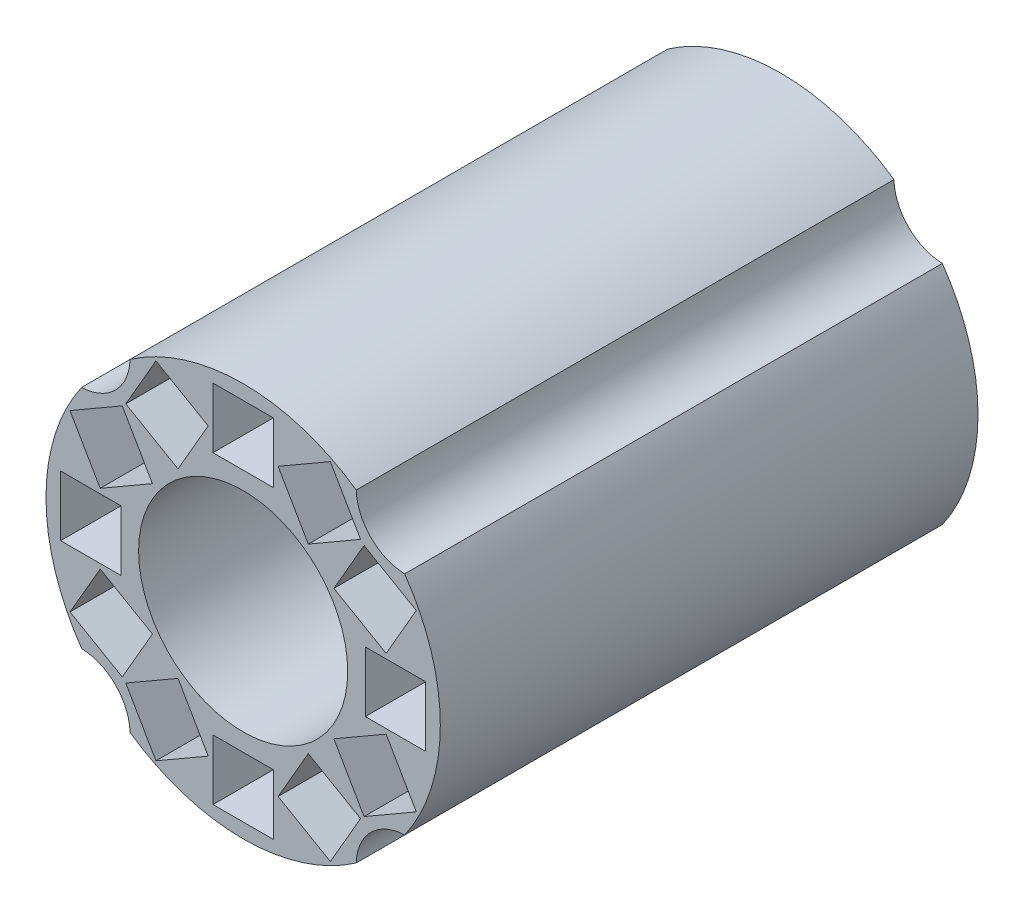
SolidWorks part; units mm, degrees
ref_plane "Front Plane" through (0, 0, 0) normal (0, 0, 1) x (1, 0, 0)
ref_plane "Top Plane" through (0, 0, 0) normal (0, 1, 0) x (1, 0, 0)
ref_plane "Right Plane" through (0, 0, 0) normal (1, 0, 0) x (0, 0, -1)
sketch "Sketch1" plane through (0, 0, 0) normal (0, 0, 1) x (1, 0, 0)
  line L0 (0, -40.3076) -> (0, 40.3076) construction
  line L5 (0, 0) -> (22.0836, 12.75) construction
  line L6 (0, 0) -> (12.75, 22.0836) construction
  line L7 (-37.9287, 0) -> (37.9287, 0) construction
  line L8 (15.1852, 10.9016) -> (20.2352, 19.6484)
  line L9 (15.1852, 10.9016) -> (23.9321, 5.8516)
  line L10 (23.9321, 5.8516) -> (28.9821, 14.5984)
  line L11 (20.2352, 19.6484) -> (28.9821, 14.5984)
  line L12 (15.1852, 10.9016) -> (28.9821, 14.5984) construction
  line L13 (23.9321, 5.8516) -> (20.2352, 19.6484) construction
  line L14 (20.45, 5.05) -> (30.55, 5.05)
  line L15 (20.45, 5.05) -> (20.45, -5.05)
  line L16 (20.45, -5.05) -> (30.55, -5.05)
  line L17 (30.55, 5.05) -> (30.55, -5.05)
  line L18 (20.45, 5.05) -> (30.55, -5.05) construction
  line L19 (20.45, -5.05) -> (30.55, 5.05) construction
  line L20 (5.8516, 23.9321) -> (14.5984, 28.9821)
  line L21 (5.8516, 23.9321) -> (10.9016, 15.1852)
  line L22 (10.9016, 15.1852) -> (19.6484, 20.2352)
  line L23 (14.5984, 28.9821) -> (19.6484, 20.2352)
  line L24 (5.8516, 23.9321) -> (19.6484, 20.2352) construction
  line L25 (10.9016, 15.1852) -> (14.5984, 28.9821) construction
  line L26 (0, 0) -> (0, 25.5) construction
  line L27 (-5.05, 30.55) -> (5.05, 30.55)
  line L28 (-5.05, 30.55) -> (-5.05, 20.45)
  line L29 (-5.05, 20.45) -> (5.05, 20.45)
  line L30 (5.05, 30.55) -> (5.05, 20.45)
  line L31 (-5.05, 30.55) -> (5.05, 20.45) construction
  line L32 (-5.05, 20.45) -> (5.05, 30.55) construction
  line L33 (-20.45, -5.05) -> (-30.55, -5.05)
  line L34 (-30.55, 5.05) -> (-30.55, -5.05)
  line L35 (-20.45, 5.05) -> (-30.55, 5.05)
  line L36 (-20.45, 5.05) -> (-20.45, -5.05)
  line L37 (-23.9321, 5.8516) -> (-28.9821, 14.5984)
  line L38 (-20.2352, 19.6484) -> (-28.9821, 14.5984)
  line L39 (-15.1852, 10.9016) -> (-20.2352, 19.6484)
  line L40 (-15.1852, 10.9016) -> (-23.9321, 5.8516)
  line L41 (-10.9016, 15.1852) -> (-19.6484, 20.2352)
  line L42 (-14.5984, 28.9821) -> (-19.6484, 20.2352)
  line L43 (-5.8516, 23.9321) -> (-14.5984, 28.9821)
  line L44 (-5.8516, 23.9321) -> (-10.9016, 15.1852)
  line L45 (23.9321, -5.8516) -> (28.9821, -14.5984)
  line L46 (20.2352, -19.6484) -> (28.9821, -14.5984)
  line L47 (15.1852, -10.9016) -> (20.2352, -19.6484)
  line L48 (15.1852, -10.9016) -> (23.9321, -5.8516)
  line L49 (10.9016, -15.1852) -> (19.6484, -20.2352)
  line L50 (14.5984, -28.9821) -> (19.6484, -20.2352)
  line L51 (5.8516, -23.9321) -> (14.5984, -28.9821)
  line L52 (5.8516, -23.9321) -> (10.9016, -15.1852)
  line L53 (-5.05, -20.45) -> (5.05, -20.45)
  line L54 (5.05, -30.55) -> (5.05, -20.45)
  line L55 (-5.05, -30.55) -> (5.05, -30.55)
  line L56 (-5.05, -30.55) -> (-5.05, -20.45)
  line L57 (-5.8516, -23.9321) -> (-10.9016, -15.1852)
  line L58 (-5.8516, -23.9321) -> (-14.5984, -28.9821)
  line L59 (-14.5984, -28.9821) -> (-19.6484, -20.2352)
  line L60 (-10.9016, -15.1852) -> (-19.6484, -20.2352)
  line L61 (-15.1852, -10.9016) -> (-23.9321, -5.8516)
  line L62 (-15.1852, -10.9016) -> (-20.2352, -19.6484)
  line L63 (-20.2352, -19.6484) -> (-28.9821, -14.5984)
  line L64 (-23.9321, -5.8516) -> (-28.9821, -14.5984)
  circle A0 centre (0, 0) radius 33
  circle A1 centre (0, 0) radius 25.5 construction
  circle A2 centre (0, 0) radius 17.5
  point P11 (0, 0)
  point P14 (0, 0)
  point P15 (25.5, 0)
  point P22 (0, 25.5)
  point P26 (12.75, 22.0836)
  dimension "D1" = 66
  dimension "D3" = 51
  dimension "D17" = 35
  dimension "D2" = 30
  dimension "D6" = 10.1
  dimension "D7" = 10.1
  dimension "D4" = 10.1
  dimension "D5" = 10.1
  dimension "D8" = 105
  dimension "D9" = 10.1
  dimension "D10" = 10.1
  dimension "D11" = 75
  dimension "D12" = 60
  dimension "D13" = 10.1
  dimension "D14" = 10.1
  dimension "D15" = 45
  dimension "D16" = 90
extrude "Boss-Extrude1" add sketch "Sketch1" along normal blind 90
sketch "Sketch2" plane through (0, 0, 90) normal (0, 0, 1) x (1, 0, 0)
  line L0 (0, 0) -> (-27.032, 18.928) construction
  line L1 (-45.9882, 0) -> (45.9882, 0) construction
  line L2 (0, -35.6846) -> (0, 35.6846) construction
  line L3 (0, 0) -> (-18.928, 27.032) construction
  circle A0 centre (0, 0) radius 33 construction
  arc A1 (-27.032, 18.928) -> (-18.928, 27.032) centre (-27.2741, 27.2741) ccw
  point P9 (0, 0)
  point P11 (0, 0)
  dimension "D3" = 8.3496
  dimension "D1" = 35
  dimension "D2" = 55
extrude "Cut-Extrude1" cut sketch "Sketch2" against normal through all both and the other way through all contours A1
mirror "Mirror1" about plane through (0, 0, 0) normal (1, 0, 0) of "Cut-Extrude1"
mirror "Mirror2" about plane through (0, 0, 0) normal (0, 1, 0) of "Mirror1", "Cut-Extrude1"
equation "\"size\"= 1.01"
equation "\"D7@Sketch1\"=\"size\""
equation "\"D6@Sketch1\"=\"size\""
equation "\"D4@Sketch1\"=\"size\""
equation "\"D5@Sketch1\"=\"size\""
equation "\"squares_radius\"= 5.1"
equation "\"D3@Sketch1\"=\"squares_radius\""
equation "\"D9@Sketch1\"=\"size\""
equation "\"D10@Sketch1\"=\"size\""
equation "\"D13@Sketch1\"=\"size\""
equation "\"D14@Sketch1\"=\"size\""
equation "\"inner_radius\"= 3.5"
equation "\"D17@Sketch1\"=\"inner_radius\""
equation "\"outer_radius\"= 6.6"
equation "\"D1@Sketch1\"=\"outer_radius\""
